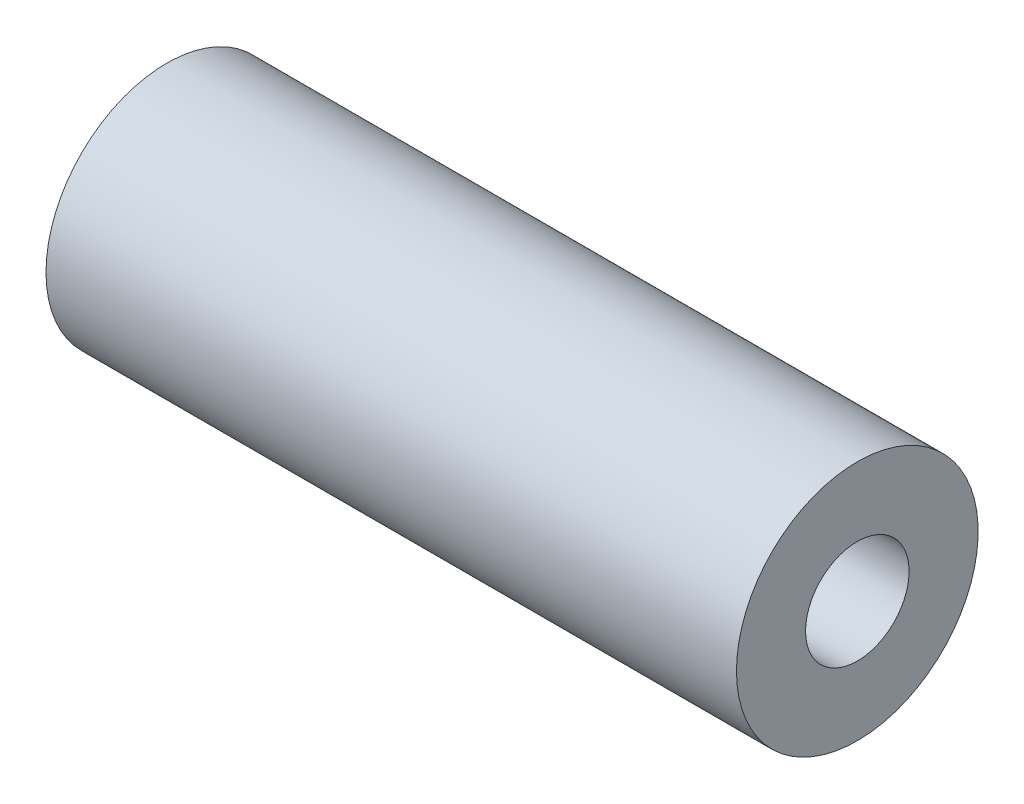
SolidWorks part; units mm, degrees
material "POM Acetal Copolymer"
ref_plane "Front Plane" through (0, 0, 0) normal (0, 0, 1) x (1, 0, 0)
ref_plane "Top Plane" through (0, 0, 0) normal (0, 1, 0) x (1, 0, 0)
ref_plane "Right Plane" through (0, 0, 0) normal (1, 0, 0) x (0, 0, -1)
sketch "Sketch1" plane through (0, 0, 0) normal (0, 0, 1) x (1, 0, 0)
  line L0 (-37.0032, 0) -> (20, 0) construction
  line L1 (-20, 7) -> (20, 7)
  line L2 (-20, 7) -> (-20, 3)
  line L3 (-20, 3) -> (20, 3)
  line L4 (20, 7) -> (20, 3)
  line L5 (20, 0) -> (20, 3) construction
  line L6 (0, 0) -> (0, 7) construction
  dimension "D1" = 6
  dimension "D2" = 40
  dimension "D3" = 14
revolve "Revolve1" add sketch "Sketch1" angle 360 about L0
